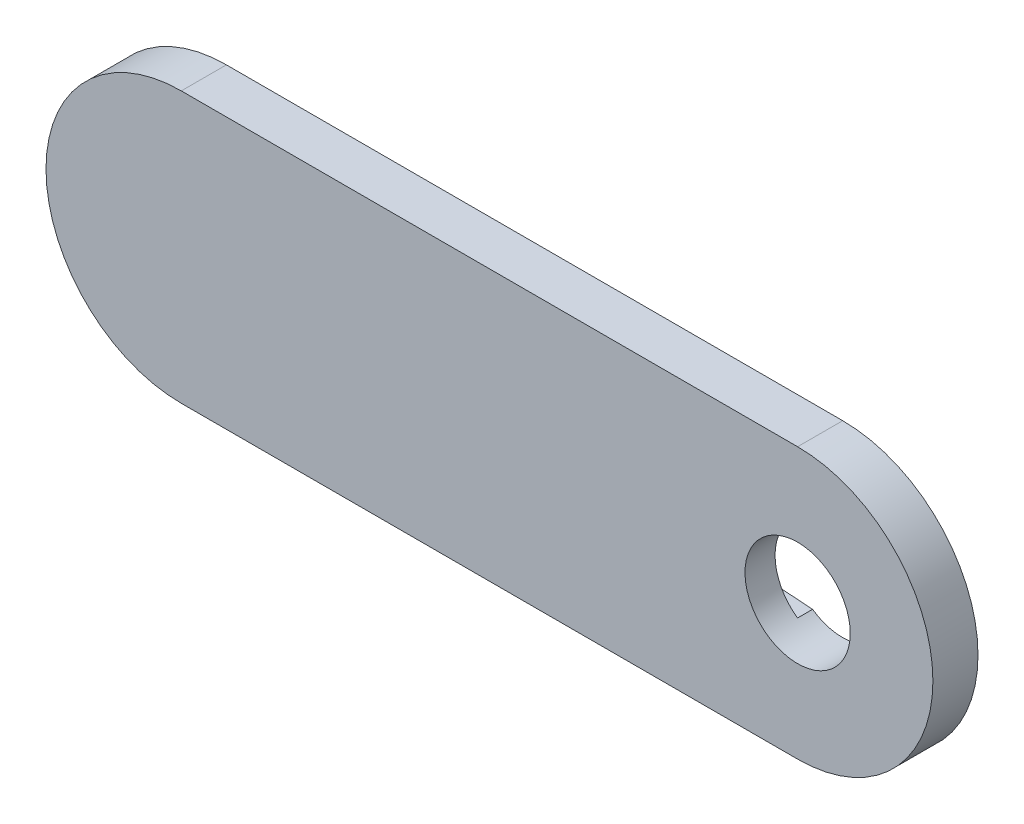
SolidWorks part; units mm, degrees
ref_plane "Alzado" through (0, 0, 0) normal (0, 0, 1) x (1, 0, 0)
ref_plane "Planta" through (0, 0, 0) normal (0, 1, 0) x (1, 0, 0)
ref_plane "Vista lateral" through (0, 0, 0) normal (1, 0, 0) x (0, 0, -1)
sketch "Corte exterior" plane through (0, 0, 0) normal (0, 0, 1) x (1, 0, 0)
  line L0 (31.3894, 4.7054) -> (72.3894, 4.7054)
  line L1 (72.3894, 22.7054) -> (31.3894, 22.7054)
  circle A0 centre (72.3894, 13.7054) radius 3.5
  arc A1 (72.3894, 4.7054) -> (72.3894, 22.7054) centre (72.3894, 13.7054) ccw
  arc A2 (31.3894, 22.7054) -> (31.3894, 4.7054) centre (31.3894, 13.7054) ccw
sketch "Grabado Superficie" plane through (0, 0, 0) normal (0, 0, 1) x (1, 0, 0)
  line L0 (70.3852, 16.5747) -> (57.9986, 15.7004)
  line L1 (57.9986, 11.7103) -> (70.3852, 10.836)
  arc A0 (57.9986, 15.7004) -> (57.9986, 11.7103) centre (58.1394, 13.7054) ccw
  arc A1 (70.3852, 16.5747) -> (70.3852, 10.836) centre (72.3894, 13.7054) ccw
extrude "Saliente-Extruir1" add sketch "Corte exterior" along normal blind 3
extrude "Cortar-Extruir1" cut sketch "Grabado Superficie" along normal blind 1
